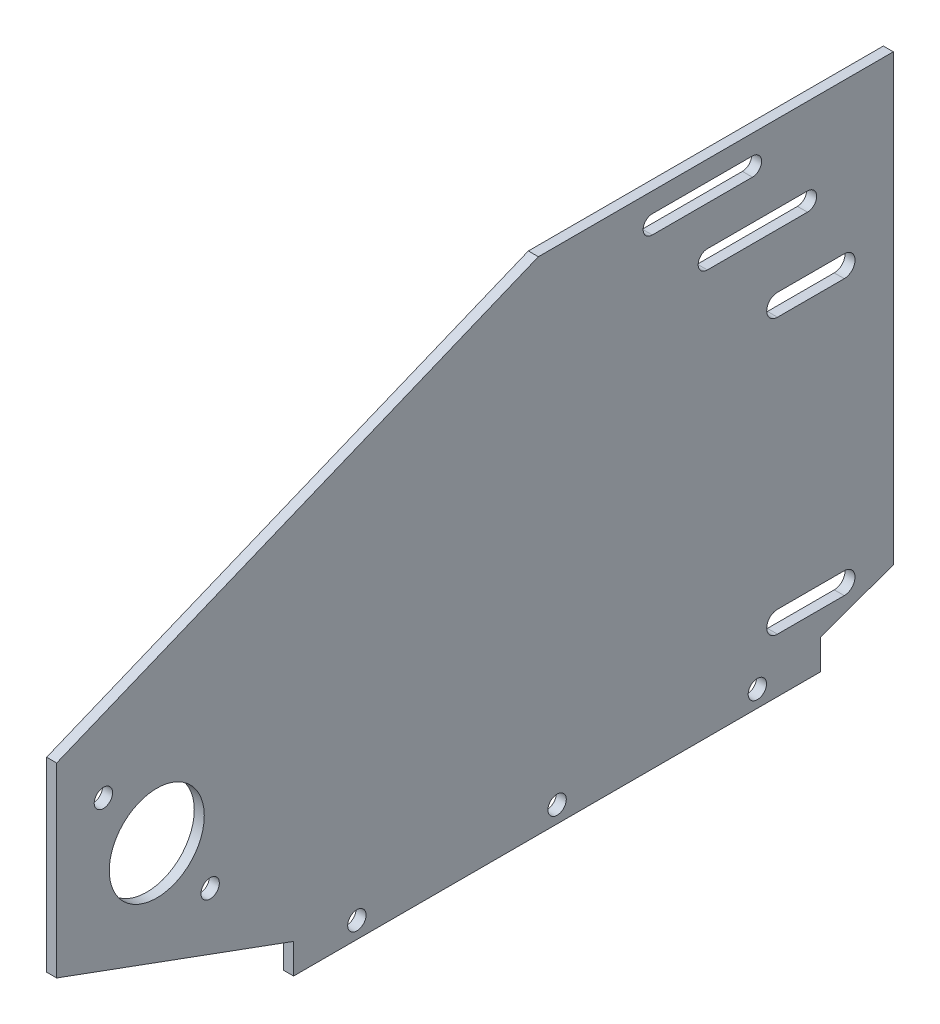
SolidWorks part; units mm, degrees
ref_plane "Front Plane" through (0, 0, 0) normal (0, 0, 1) x (1, 0, 0)
ref_plane "Top Plane" through (0, 0, 0) normal (0, 1, 0) x (1, 0, 0)
ref_plane "Right Plane" through (0, 0, 0) normal (1, 0, 0) x (0, 0, -1)
sketch "Sketch1" plane through (0, 0, 0) normal (1, 0, 0) x (0, 0, -1)
  line L1 (0, 0) -> (300, 0)
  line L2 (0, 0) -> (0, 150)
  line L3 (0, 150) -> (300, 150)
  line L4 (300, 0) -> (300, 150)
  circle A0 centre (30, 55) radius 14.235
  dimension "D1" = 300
  dimension "D5" = 28.47
  dimension "D4" = 55
  dimension "D2" = 150
  dimension "D3" = 30
extrude "Boss-Extrude1" add sketch "Sketch1" along normal blind 3
sketch "Sketch2" plane through (0, 0, 0) normal (-1, 0, 0) x (0, 0, 1)
  line L0 (-300, 0) -> (-300, 150) construction
  line L3 (-216, 101.7084) -> (-236, 101.7084) construction
  line L4 (-216, 98.4784) -> (-236, 98.4784)
  line L5 (-216, 104.9384) -> (-236, 104.9384)
  line L11 (-236, 19.4567) -> (-216, 19.4567) construction
  line L12 (-236, 22.6817) -> (-216, 22.6817)
  line L13 (-236, 16.2317) -> (-216, 16.2317)
  line L14 (0, 0) -> (-300, 0) construction
  line L17 (0, 150) -> (0, 0) construction
  arc A3 (-216, 98.4784) -> (-216, 104.9384) centre (-216, 101.7084) ccw
  arc A4 (-236, 104.9384) -> (-236, 98.4784) centre (-236, 101.7084) ccw
  arc A9 (-236, 22.6817) -> (-236, 16.2317) centre (-236, 19.4567) ccw
  arc A10 (-216, 16.2317) -> (-216, 22.6817) centre (-216, 19.4567) ccw
  circle A12 centre (-10, 110) radius 3.225
  point P0 (0, 0)
  point P9 (-226, 101.7084)
  point P34 (-226, 19.4567)
  dimension "D4" = 64
  dimension "D14" = 6.45
  dimension "D3" = 20
  dimension "D5" = 20
  dimension "D20" = 10
  dimension "D21" = 110
extrude "Cut-Extrude1" cut sketch "Sketch2" against normal up to next
sketch "Sketch3" plane through (3, 0, 0) normal (1, 0, 0) x (0, 0, -1)
  line L0 (0, 150) -> (0, 0) construction
  line L1 (0, 0) -> (300, 0) construction
  circle A1 centre (14.0057, 74.7318) radius 2.75
  circle A2 centre (45.9943, 35.2682) radius 2.75
  dimension "D5" = 5.5
  dimension "D6" = 5.5
  dimension "D1" = 14.0057
  dimension "D2" = 45.9943
  dimension "D3" = 74.7318
  dimension "D4" = 35.2682
extrude "Cut-Extrude2" cut sketch "Sketch3" against normal through all
sketch "Sketch4" plane through (3, 0, 0) normal (1, 0, 0) x (0, 0, -1)
  line L0 (71, 9) -> (0, 35)
  line L1 (0, 150) -> (0, 0) construction
  line L2 (0, 35) -> (0, 0)
  line L3 (0, 0) -> (71, 0)
  line L4 (0, 0) -> (300, 0) construction
  line L5 (71, 9) -> (71, 0) construction
  line L6 (71, 0) -> (71, 9)
  dimension "D1" = 35
  dimension "D2" = 71
  dimension "D3" = 9
extrude "Cut-Extrude3" cut sketch "Sketch4" against normal through all
sketch "Sketch5" plane through (3, 0, 0) normal (1, 0, 0) x (0, 0, -1)
  line L0 (228.924, 9) -> (250.718, 16.8759)
  line L4 (71, 0) -> (300, 0) construction
  line L5 (228.924, 9) -> (228.924, 0) construction
  line L6 (228.924, 0) -> (228.924, 9)
  line L7 (250.718, 16.8759) -> (250.718, 150)
  line L8 (300, 150) -> (0, 150) construction
  line L9 (250.718, 150) -> (312.6604, 150)
  line L10 (312.6604, 150) -> (312.6604, -2.8296)
  line L11 (312.6604, -2.8296) -> (228.924, 0)
extrude "Cut-Extrude4" cut sketch "Sketch5" against normal blind 10
sketch "Sketch6" plane through (3, 0, 0) normal (1, 0, 0) x (0, 0, -1)
  line L2 (146.1658, 150.7457) -> (0, 90.7963)
  line L5 (0, 90.7963) -> (-32.5537, 170.1671)
  line L11 (-32.5537, 170.1671) -> (146.1658, 150.7457)
extrude "Cut-Extrude5" cut sketch "Sketch6" against normal blind 10
sketch "Sketch7" plane through (0, 0, 0) normal (-1, 0, 0) x (0, 0, 1)
  line L0 (-71, 0) -> (-228.924, 0) construction
  circle A0 centre (-209.962, 5) radius 2.75
  circle A1 centre (-149.962, 5) radius 2.75
  circle A2 centre (-89.962, 5) radius 2.75
  point P8 (-149.962, 0)
  dimension "D1" = 5.5
  dimension "D2" = 5.5
  dimension "D3" = 5.5
  dimension "D4" = 60
  dimension "D5" = 60
  dimension "D6" = 5
extrude "Cut-Extrude6" cut sketch "Sketch7" against normal through all
sketch "Sketch8" plane through (0, 0, 0) normal (-1, 0, 0) x (0, 0, 1)
  line L0 (-208.4859, 141.3281) -> (-178.4859, 141.3281) construction
  line L1 (-208.4859, 144.0781) -> (-178.4859, 144.0781)
  line L2 (-208.4859, 138.5781) -> (-178.4859, 138.5781)
  line L3 (-224.9828, 124) -> (-194.9828, 124) construction
  line L4 (-224.9828, 126.75) -> (-194.9828, 126.75)
  line L5 (-224.9828, 121.25) -> (-194.9828, 121.25)
  line L6 (-250.718, 150) -> (-144.3477, 150) construction
  arc A0 (-208.4859, 144.0781) -> (-208.4859, 138.5781) centre (-208.4859, 141.3281) ccw
  arc A1 (-178.4859, 138.5781) -> (-178.4859, 144.0781) centre (-178.4859, 141.3281) ccw
  arc A2 (-224.9828, 126.75) -> (-224.9828, 121.25) centre (-224.9828, 124) ccw
  arc A3 (-194.9828, 121.25) -> (-194.9828, 126.75) centre (-194.9828, 124) ccw
  point P2 (-193.4859, 141.3281)
  point P7 (-209.9828, 124)
  point P14 (-189.6674, 144.898)
  point P15 (-193.4859, 141.3281)
  point P16 (-209.9828, 118.1676)
  dimension "D1" = 2.75
  dimension "D2" = 2.75
  dimension "D5" = 26
  dimension "D3" = 30
  dimension "D4" = 30
extrude "Cut-Extrude7" cut sketch "Sketch8" against normal blind 10
